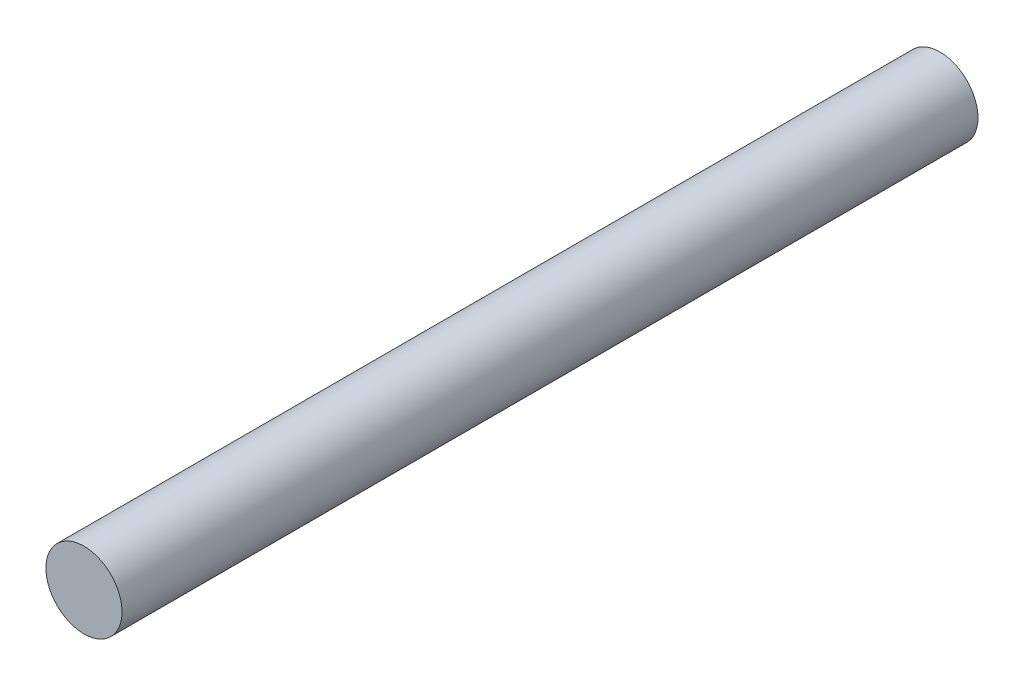
SolidWorks part; units mm, degrees
ref_plane "Front Plane" through (0, 0, 0) normal (0, 0, 1) x (1, 0, 0)
ref_plane "Top Plane" through (0, 0, 0) normal (0, 1, 0) x (1, 0, 0)
ref_plane "Right Plane" through (0, 0, 0) normal (1, 0, 0) x (0, 0, -1)
sketch "Sketch1" plane through (0, 0, 0) normal (0, 0, 1) x (1, 0, 0)
  circle A0 centre (0, 0) radius 20
extrude "Boss-Extrude1" add sketch "Sketch1" along normal blind 450
